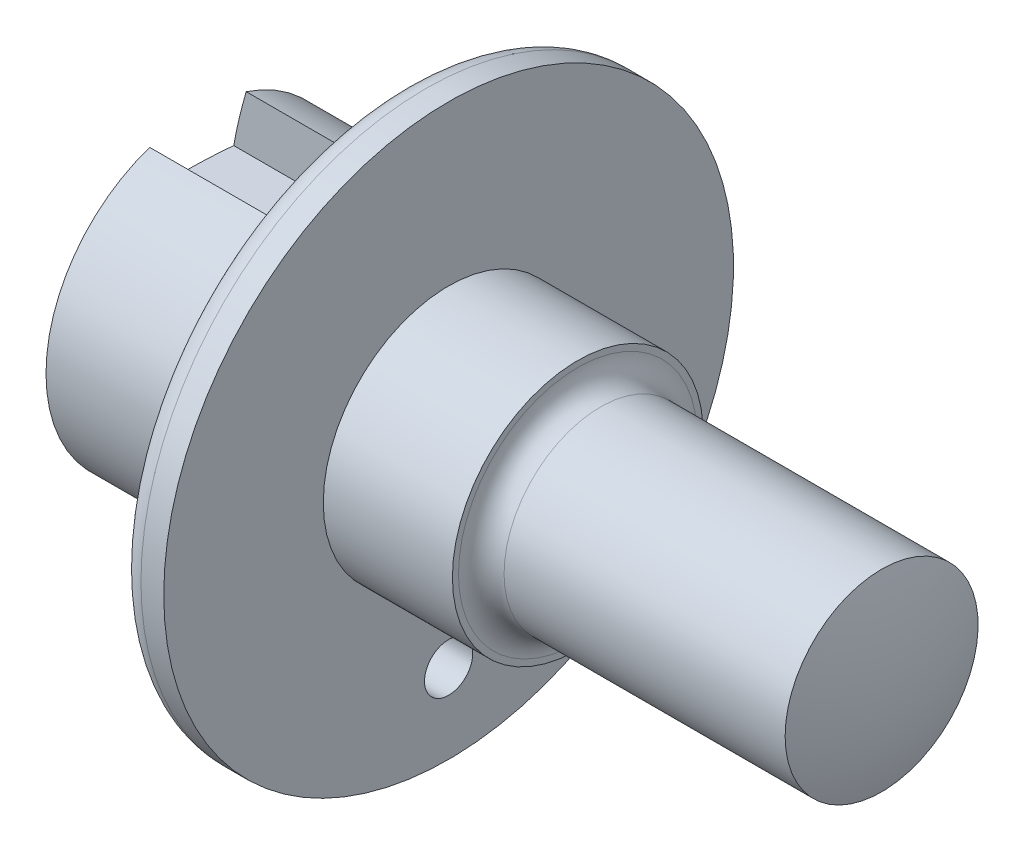
SolidWorks part; units mm, degrees
material "AISI 1020"
ref_plane "Plano frontal" through (0, 0, 0) normal (0, 0, 1) x (1, 0, 0)
ref_plane "Plano superior" through (0, 0, 0) normal (0, 1, 0) x (1, 0, 0)
ref_plane "Plano direito" through (0, 0, 0) normal (1, 0, 0) x (0, 0, -1)
sketch "Esboço1" plane through (0, 0, 0) normal (0, 0, 1) x (1, 0, 0)
  line L0 (-47.5, 0) -> (47.5, 0) construction
  line L1 (45.5, 12.7) -> (8.5, 12.7)
  line L2 (5.5, 15.7) -> (5.5, 16.5)
  line L3 (5.5, 16.5) -> (-11.5, 16.5)
  line L4 (-11.5, 16.5) -> (-11.5, 37.5)
  line L5 (-11.5, 37.5) -> (-17.5, 37.5)
  line L6 (-17.5, 37.5) -> (-17.5, 20)
  line L7 (-17.5, 20) -> (-44.5, 20)
  line L8 (-47.5, 0) -> (-47.5, 47.235) construction
  line L9 (47.5, 0) -> (47.5, 48.5204) construction
  line L10 (-47.5, 0) -> (47.5, 0)
  arc A0 (47.5, 0) -> (45.5, 12.7) centre (6.1775, 0) ccw
  arc A1 (-47.5, 0) -> (-44.5, 20) centre (20.6667, 0) cw
  arc A2 (8.5, 12.7) -> (5.5, 15.7) centre (8.5, 15.7) cw
  dimension "D1" = 3
  dimension "D2" = 2
  dimension "D3" = 95
  dimension "D4" = 39
  dimension "D5" = 33
  dimension "D6" = 75
  dimension "D7" = 40
  dimension "D8" = 30
  dimension "D9" = 3
  dimension "D10" = 6
  dimension "D11" = 25.4
revolve "Revolução1" add sketch "Esboço1" angle 360 about L10
fillet "Filete1" radius 3 1 edges at (-17.5, 0, 37.5)
ref_plane "Plano1" through (-47.5, 0, 0) normal (-1, 0, 0) x (0, 0, 1)
sketch "Esboço2" plane through (-47.5, 0, 0) normal (-1, 0, 0) x (0, 0, 1)
  line L0 (0, 20) -> (0, 0) construction
  line L1 (-6.35, 28) -> (6.35, 28)
  line L2 (-6.35, 28) -> (-6.35, 12)
  line L3 (-6.35, 12) -> (6.35, 12)
  line L4 (6.35, 28) -> (6.35, 12)
  line L5 (-6.35, 28) -> (6.35, 12) construction
  line L6 (-6.35, 12) -> (6.35, 28) construction
  circle A0 centre (0, 0) radius 20 construction
  circle A1 centre (0, 0) radius 20 construction
  point P0 (0, 20)
  dimension "D1" = 8
  dimension "D2" = 12.7
extrude "Corte-extrusão1" cut sketch "Esboço2" against normal blind 20
sketch "Esboço3" plane through (-17.5, 0, 0) normal (-1, 0, 0) x (0, 0, 1)
  circle A0 centre (0, -27) radius 3.175
  dimension "D1" = 27
  dimension "D2" = 6.35
extrude "Corte-extrusão2" cut sketch "Esboço3" against normal blind 20
